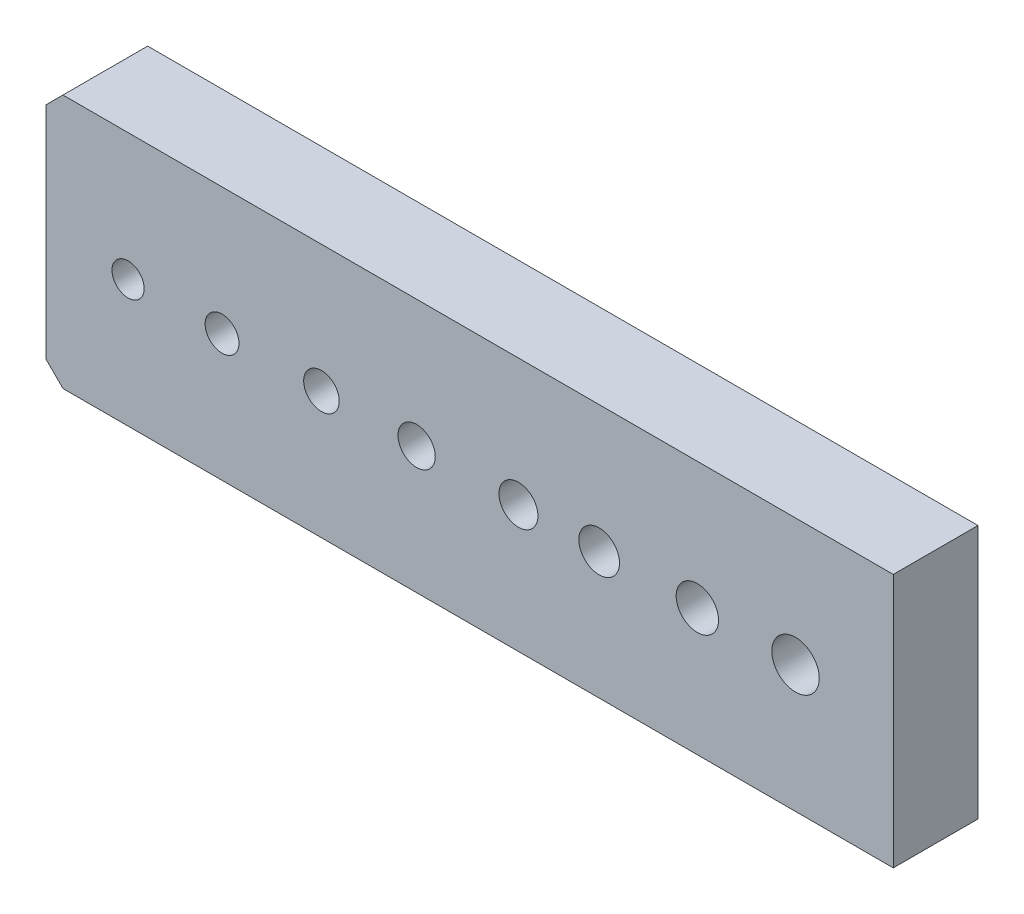
SolidWorks part; units mm, degrees
ref_plane "Front Plane" through (0, 0, 0) normal (0, 0, 1) x (1, 0, 0)
ref_plane "Top Plane" through (0, 0, 0) normal (0, 1, 0) x (1, 0, 0)
ref_plane "Right Plane" through (0, 0, 0) normal (1, 0, 0) x (0, 0, -1)
sketch "Sketch1" plane through (0, 0, 0) normal (0, 0, 1) x (1, 0, 0)
  line L1 (-25, -7.5) -> (25, -7.5)
  line L2 (-25, -7.5) -> (-25, 7.5)
  line L3 (-25, 7.5) -> (25, 7.5)
  line L4 (25, -7.5) -> (25, 7.5)
  line L5 (-25, -7.5) -> (25, 7.5) construction
  line L6 (-25, 7.5) -> (25, -7.5) construction
  point P0 (0, 0)
  dimension "D1" = 15
  dimension "D2" = 50
extrude "Boss-Extrude1" add sketch "Sketch1" along normal blind 5
sketch "Sketch2" plane through (0, 0, 5) normal (0, 0, 1) x (1, 0, 0)
  line L0 (-1000, 0) -> (49000, 0) construction
  circle A0 centre (-20.1567, 0) radius 0.95
  circle A1 centre (-14.6109, 0) radius 1
  circle A2 centre (-8.7452, 0) radius 1.05
  circle A3 centre (-3.1284, 0) radius 1.1
  circle A4 centre (2.8795, 0) radius 1.15
  circle A5 centre (7.6432, 0) radius 1.2
  circle A6 centre (13.4378, 0) radius 1.25
  circle A7 centre (19.2324, 0) radius 1.4
  point P19 (-20.1567, 0)
  point P20 (-14.6109, 0)
  point P21 (-8.7452, 0)
  point P22 (-3.1284, 0)
  point P23 (19.2324, 0)
  point P24 (13.4378, 0)
  point P25 (7.6432, 0)
  point P26 (2.8795, 0)
  dimension "D1" = 1.9
  dimension "D2" = 2
  dimension "D3" = 2.1
  dimension "D4" = 2.2
  dimension "D5" = 2.3
  dimension "D6" = 2.4
  dimension "D7" = 2.5
  dimension "D8" = 2.8
extrude "Cut-Extrude1" cut sketch "Sketch2" against normal through all
chamfer "Chamfer1" distance 1 angle 45 2 edges at (-25, -7.5, 2.5) (-25, 7.5, 2.5)
